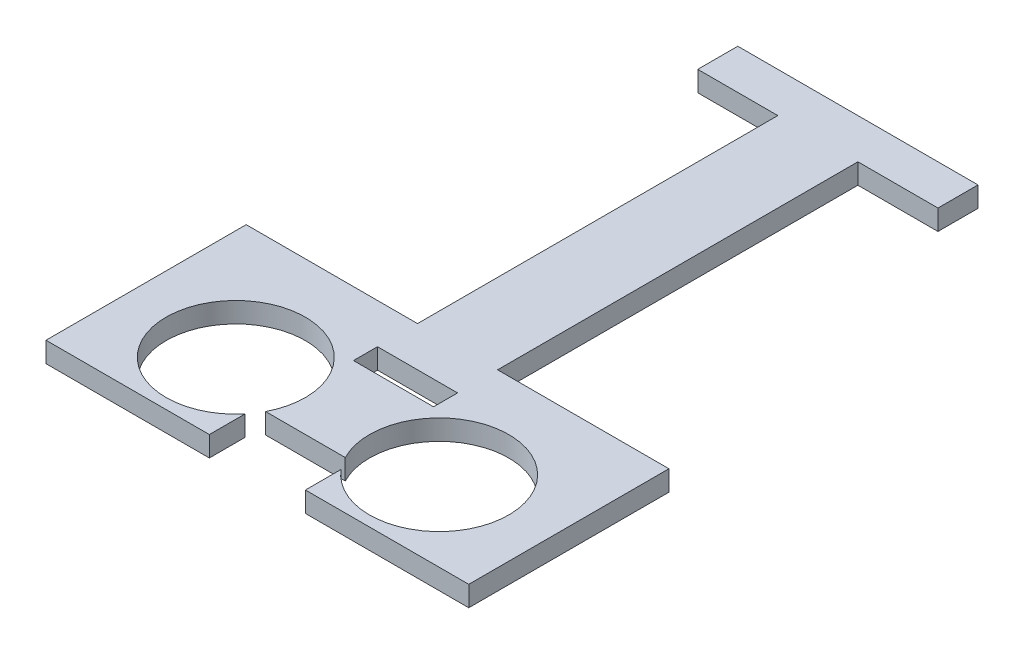
SolidWorks part; units mm, degrees
ref_plane "Front Plane" through (0, 0, 0) normal (0, 0, 1) x (1, 0, 0)
ref_plane "Top Plane" through (0, 0, 0) normal (0, 1, 0) x (1, 0, 0)
ref_plane "Right Plane" through (0, 0, 0) normal (1, 0, 0) x (0, 0, -1)
sketch "Sketch1" plane through (0, 0, 0) normal (0, 1, 0) x (1, 0, 0)
  line L0 (-34.5501, -25.1002) -> (44.6892, -25.1002) construction
  line L1 (-2.7518, 24.8998) -> (7.2482, 24.8998)
  line L2 (-2.7518, 24.8998) -> (-2.7518, -20.1002)
  line L3 (-2.7518, -20.1002) -> (7.2482, -20.1002)
  line L4 (7.2482, 24.8998) -> (7.2482, -20.1002)
  line L5 (-12.7518, 24.8998) -> (17.2482, 24.8998)
  line L6 (-12.7518, 24.8998) -> (-12.7518, 29.8998)
  line L7 (-12.7518, 29.8998) -> (17.2482, 29.8998)
  line L8 (17.2482, 24.8998) -> (17.2482, 29.8998)
  line L9 (-24.1518, -20.1002) -> (28.6482, -20.1002)
  line L10 (-24.1518, -20.1002) -> (-24.1518, -45.1002)
  line L11 (-24.1518, -45.1002) -> (28.6482, -45.1002)
  line L12 (28.6482, -20.1002) -> (28.6482, -45.1002)
  line L14 (-2.7518, -25.1002) -> (7.2482, -25.1002)
  line L15 (-2.7518, -25.1002) -> (-2.7518, -28.1002)
  line L16 (-2.7518, -28.1002) -> (7.2482, -28.1002)
  line L17 (7.2482, -25.1002) -> (7.2482, -28.1002)
  line L18 (-3.7518, -39.1002) -> (8.2482, -39.1002)
  line L19 (-3.7518, -39.1002) -> (-3.7518, -45.1002)
  line L20 (-3.7518, -45.1002) -> (8.2482, -45.1002)
  line L21 (8.2482, -39.1002) -> (8.2482, -45.1002)
  circle A0 centre (-10.4518, -35.1002) radius 8.7
  circle A1 centre (14.9482, -35.1002) radius 8.7
  dimension "D19" = 17.4
  dimension "D20" = 17.4
  dimension "D1" = 30
  dimension "D2" = 5
  dimension "D3" = 45
  dimension "D4" = 0
  dimension "D5" = 10
  dimension "D6" = 10
  dimension "D7" = 0
  dimension "D8" = 52.8
  dimension "D9" = 25
  dimension "D10" = 5
  dimension "D11" = 21.4
  dimension "D12" = 10
  dimension "D13" = 21.4
  dimension "D14" = 3
  dimension "D15" = 12
  dimension "D16" = 20.4
  dimension "D17" = 6
  dimension "D18" = 13.7
  dimension "D21" = 10
  dimension "D22" = 10
  dimension "D23" = 25.4
  dimension "D24" = 79.2393
extrude "Boss-Extrude2" add sketch "Sketch1" along normal blind 2.54 contours L5 L8 L7 L6 L1 | L4 L1 L2 L3 | L10 L0 L14 L12 L9 L3 | L0 L10 L11 L19 A0 L18 A1 L21 L12 L17 L16 L15
